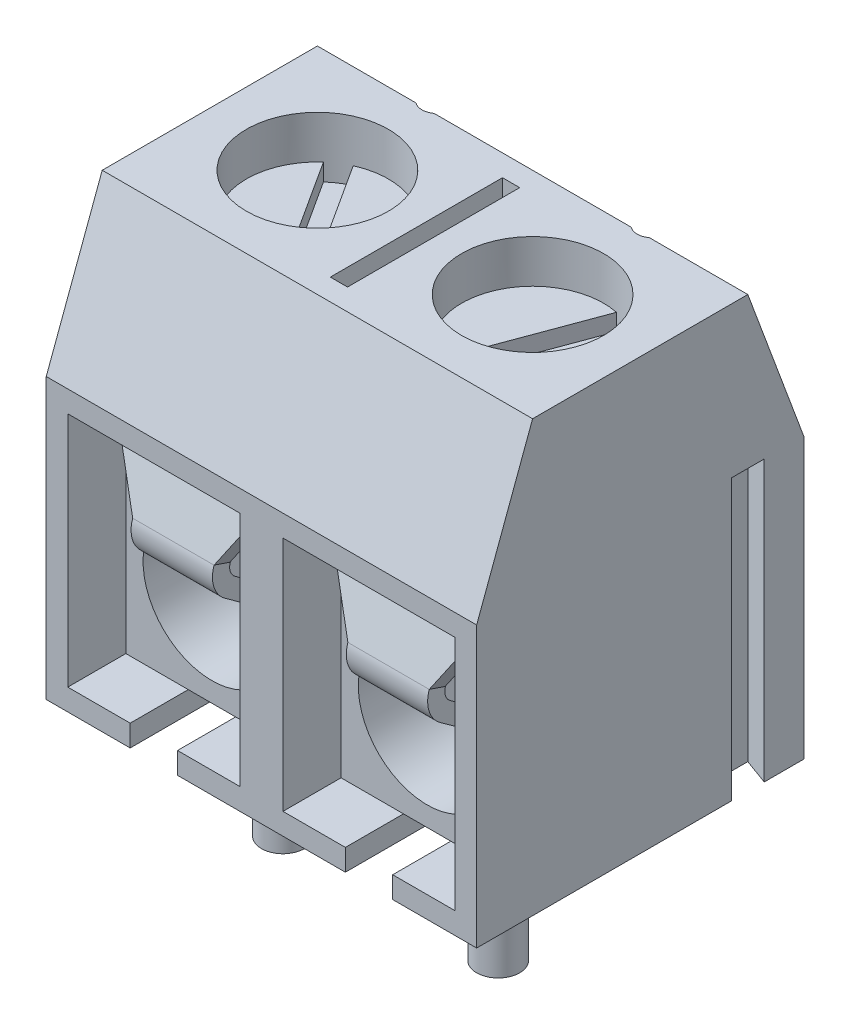
SolidWorks part; units mm, degrees
ref_plane "Front Plane" through (0, 0, 0) normal (0, 0, 1) x (1, 0, 0)
ref_plane "Top Plane" through (0, 0, 0) normal (0, 1, 0) x (1, 0, 0)
ref_plane "Right Plane" through (0, 0, 0) normal (1, 0, 0) x (0, 0, -1)
sketch "Sketch1" plane through (0, 0, 0) normal (0, 1, 0) x (1, 0, 0)
  line L1 (-5, 3.8) -> (5, 3.8)
  line L2 (-5, 3.8) -> (-5, -3.8)
  line L3 (-5, -3.8) -> (5, -3.8)
  line L4 (5, 3.8) -> (5, -3.8)
  dimension "D1" = 10
  dimension "D2" = 5
  dimension "D3" = 7.6
  dimension "D4" = 3.8
extrude "Extrude1" add sketch "Sketch1" along normal blind 10
sketch "Sketch2" plane through (0, 0, 0) normal (1, 0, 0) x (0, 0, -1)
  line L0 (2.5, 10) -> (3.8, 6.5)
  line L1 (3.8, 10) -> (-3.8, 10) construction
  line L2 (3.8, 10) -> (3.8, 0) construction
  line L3 (3.8, 6.5) -> (-3.8, 6.5) construction
  line L4 (-3.8, 10) -> (-3.8, 0) construction
  line L5 (-3.8, 6.5) -> (-2.5, 10)
  line L6 (-2.5, 10) -> (2.5, 10)
  line L7 (3.8, 6.5) -> (3.8, 0)
  line L8 (3.8, 0) -> (-3.8, 0)
  line L9 (-3.8, 0) -> (-3.8, 6.5)
  dimension "D1" = 5
  dimension "D2" = 2.5
  dimension "D3" = 3.5
extrude "Cut-Extrude1" cut sketch "Sketch2" against normal through all and the other way through all flip side to cut
sketch "Sketch3" plane through (0, 10, 0) normal (0, 1, 0) x (-1, 0, 0)
  line L0 (5, -2.5) -> (-5, -2.5) construction
  line L1 (0.2, -2) -> (-0.2, -2)
  line L2 (0.2, -2) -> (0.2, 2)
  line L3 (0.2, 2) -> (-0.2, 2)
  line L4 (-0.2, -2) -> (-0.2, 2)
  circle A0 centre (2.5, 0) radius 1.65
  circle A1 centre (-2.5, 0) radius 1.65
  circle A2 centre (2.5, -2.78) radius 0.35
  circle A3 centre (-2.5, -2.78) radius 0.35
  dimension "D7" = 3.3
  dimension "D8" = 0.7
  dimension "D1" = 0.4
  dimension "D2" = 0.2
  dimension "D3" = 4
  dimension "D4" = 2
  dimension "D5" = 2.5
  dimension "D6" = 2.5
  dimension "D9" = 0.28
extrude "Cut-Extrude2" cut sketch "Sketch3" against normal blind 4
sketch "Sketch4" plane through (0, 0, 3.8) normal (0, 0, 1) x (1, 0, 0)
  line L0 (-5, 6.5) -> (-5, 0) construction
  line L1 (-4.5, 6) -> (-0.5, 6)
  line L2 (-4.5, 6) -> (-4.5, 0.5)
  line L3 (-4.5, 0.5) -> (-0.5, 0.5)
  line L4 (-0.5, 6) -> (-0.5, 0.5)
  line L5 (0.5, 6) -> (4.5, 6)
  line L6 (0.5, 6) -> (0.5, 0.5)
  line L7 (0.5, 0.5) -> (4.5, 0.5)
  line L8 (4.5, 6) -> (4.5, 0.5)
  line L9 (-5, 6.5) -> (5, 6.5) construction
  line L10 (-5, 0) -> (5, 0) construction
  line L11 (5, 6.5) -> (5, 0) construction
  dimension "D1" = 0.5
  dimension "D2" = 0.5
  dimension "D3" = 0.5
  dimension "D4" = 1
  dimension "D5" = 0.5
extrude "Cut-Extrude3" cut sketch "Sketch4" against normal offset from surface (5.6 mm away) 2 up to face at (0, 3.25, -3.8)
sketch "Sketch5" plane through (0, 0, -1.8) normal (0, 0, 1) x (1, 0, 0)
  line L0 (-4.5, 5.6) -> (-0.5, 5.6)
  line L1 (0.5, 5.6) -> (4.5, 5.6)
  line L2 (-4.5, 5.6) -> (-4.5, 0.5)
  line L3 (-0.5, 5.6) -> (-0.5, 6) construction
  line L4 (-4.5, 6) -> (-4.5, 0.5)
  line L5 (-4.5, 0.5) -> (-0.5, 0.5)
  line L6 (-0.5, 0.5) -> (-0.5, 6)
  line L7 (-0.5, 6) -> (-4.5, 6)
  line L8 (-4.5, 6) -> (-4.5, 5.6) construction
  line L9 (-4.5, 0.5) -> (-0.5, 0.5)
  line L10 (-0.5, 0.5) -> (-0.5, 5.6)
  line L11 (-0.5, 6) -> (-4.5, 6) construction
  line L12 (0.5, 6) -> (0.5, 0.5)
  line L13 (0.5, 0.5) -> (4.5, 0.5)
  line L14 (4.5, 0.5) -> (4.5, 6)
  line L15 (4.5, 6) -> (0.5, 6)
  line L16 (0.5, 6) -> (0.5, 5.6) construction
  line L17 (0.5, 0.5) -> (4.5, 0.5)
  line L18 (4.5, 0.5) -> (4.5, 5.6)
  line L19 (4.5, 6) -> (0.5, 6) construction
  line L20 (0.5, 5.6) -> (0.5, 0.5)
  line L21 (4.5, 5.6) -> (4.5, 6) construction
  dimension "D3" = 0.4
  dimension "D1" = 0
  dimension "D2" = 0
extrude "Extrude2" add sketch "Sketch5" along normal offset from surface (4.25 mm away) 1.35 up to face at (2.5, 3.25, 3.8)
sketch "Sketch6" plane through (0, 0, 2.45) normal (0, 0, 1) x (1, 0, 0)
  circle A0 centre (-2.5, 2.5543) radius 1.6
  circle A1 centre (2.5, 2.5543) radius 1.6
  dimension "D1" = 3.2
extrude "Cut-Extrude4" cut sketch "Sketch6" against normal up to surface (4.25 mm away) up to face at (-2.5, 5.8, -1.8)
ref_plane "Plane1" through (-2.5, 0, 0) normal (1, 0, 0) x (0, 0, -1)
ref_plane "Plane2" through (2.5, 0, 0) normal (1, 0, 0) x (0, 0, -1)
sketch "Sketch7" plane through (0, 0, 0) normal (0, 1, 0) x (1, 0, 0)
  line L0 (-5, 2.5) -> (-5, -2.5) construction
  line L1 (-5.6, 3.1) -> (-5, 2.8816)
  line L2 (-5.6, 3.1) -> (-5.6, 1.9)
  line L3 (-5.6, 1.9) -> (-5, 2.1184)
  line L4 (-5, 2.8816) -> (-5, 2.1184)
  line L5 (5, 3.8) -> (-5, 3.8) construction
  dimension "D1" = 1.2
  dimension "D2" = 70
  dimension "D3" = 70
  dimension "D4" = 0.6
  dimension "D5" = 1.9
extrude "Extrude3" add sketch "Sketch7" along normal up to vertex (6.5 mm away) up to point (-5, 6.5, -3.8)
sketch "Sketch9" plane through (0, 0, 0) normal (0, 1, 0) x (1, 0, 0)
  line L0 (5, -3.8) -> (5, 3.8) construction
  line L8 (5, 2.8816) -> (4.4, 3.1)
  line L9 (5, 2.1184) -> (5, 2.8816)
  line L10 (4.4, 1.9) -> (5, 2.1184)
  line L11 (4.4, 3.1) -> (4.4, 1.9)
extrude "Cut-Extrude5" cut sketch "Sketch9" along normal up to vertex (6.5 mm away) up to point (5, 6.5, -3.8)
sketch "Sketch10" plane through (0, 0, 3.8) normal (0, 0, 1) x (1, 0, 0)
  line L0 (-4.5, 0.5) -> (-0.5, 0.5) construction
  line L1 (-3.05, 0.5) -> (-1.95, 0.5)
  line L2 (-3.05, 0.5) -> (-3.05, 0)
  line L3 (-3.05, 0) -> (-1.95, 0)
  line L4 (-1.95, 0.5) -> (-1.95, 0)
  line L5 (-5, 0) -> (5, 0) construction
  line L6 (0.5, 0.5) -> (4.5, 0.5) construction
  line L7 (1.95, 0.5) -> (3.05, 0.5)
  line L8 (1.95, 0.5) -> (1.95, 0)
  line L9 (1.95, 0) -> (3.05, 0)
  line L10 (3.05, 0.5) -> (3.05, 0)
  dimension "D1" = 1.1
  dimension "D2" = 0.55
  dimension "D3" = 0.55
extrude "Cut-Extrude6" cut sketch "Sketch10" against normal blind 3.6
sketch "Sketch11" plane through (0, 0.5, 0) normal (0, -1, 0) x (1, 0, 0)
  line L0 (-2.5, -1.8) -> (-2.5, 2.45) construction
  line L1 (2.5, -1.8) -> (2.5, 2.45) construction
  line L2 (-3.05, 0.2) -> (-1.95, 0.2) construction
  circle A0 centre (-2.5, 0.8) radius 0.5
  circle A1 centre (2.5, 0.8) radius 0.5
  dimension "D1" = 0.6
extrude "Extrude4" add sketch "Sketch11" along normal blind 3.5
sketch "Sketch12" plane through (0, 6, 0) normal (0, -1, 0) x (1, 0, 0)
  circle A0 centre (2.5, 0) radius 1.65 construction
  circle A1 centre (-2.5, 0) radius 1.65 construction
  circle A2 centre (2.5, 0) radius 1.65
  circle A3 centre (-2.5, 0) radius 1.65
extrude "Extrude5" add sketch "Sketch12" against normal offset from surface (3 mm away) 1 up to face at (0, 10, -1.2325)
sketch "Sketch13" plane through (0, 9, 0) normal (0, 1, 0) x (-1, 0, 0)
  line L1 (3.5943, -1.2349) -> (1.8258, 1.506)
  line L2 (3.1742, -1.506) -> (1.4057, 1.2349)
  line L5 (-2.8322, -1.6162) -> (-1.699, 1.4425)
  line L6 (-3.301, -1.4425) -> (-2.1678, 1.6162)
  circle A0 centre (-2.5, 0) radius 1.65 construction
  circle A1 centre (2.5, 0) radius 1.65 construction
  arc A2 (-1.699, 1.4425) -> (-2.1678, 1.6162) centre (-2.5, 0) ccw
  arc A3 (1.8258, 1.506) -> (1.4057, 1.2349) centre (2.5, 0) ccw
  arc A4 (-3.301, -1.4425) -> (-2.8322, -1.6162) centre (-2.5, 0) ccw
  arc A5 (3.1742, -1.506) -> (3.5943, -1.2349) centre (2.5, 0) ccw
  dimension "D1" = 0.5
  dimension "D2" = 0.5
extrude "Cut-Extrude7" cut sketch "Sketch13" against normal blind 0.4
sketch "Sketch14" plane through (-2.5, 0, 0) normal (-1, 0, 0) x (0, 0, 1)
  line L0 (2.45, 5.6) -> (3.0389, 3.8617)
  line L1 (3.0389, 3.8617) -> (0.1672, 1.7876)
  line L2 (0.1672, 1.7876) -> (-0.5464, 2.0974)
  line L3 (-0.5464, 2.0974) -> (-0.7057, 1.7305)
  line L4 (-0.7057, 1.7305) -> (0.2168, 1.33)
  line L5 (0.2168, 1.33) -> (3.5125, 3.7103)
  line L6 (-1.8, 5.6) -> (2.45, 5.6)
  line L7 (2.45, 5.6) -> (2.45, 0.5)
  line L8 (2.45, 0.5) -> (3.8, 0.5)
  line L9 (3.8, 0.5) -> (3.8, 6)
  line L10 (3.8, 6) -> (-1.8, 6)
  line L11 (-1.8, 6) -> (-1.8, 5.6)
  line L12 (-1.8, 5.6) -> (2.45, 5.6)
  line L13 (3.5125, 3.7103) -> (2.7368, 6)
  line L14 (2.7368, 6) -> (-1.8, 6)
  line L17 (-1.8, 6) -> (-1.8, 5.6)
  dimension "D2" = 0.4
  dimension "D3" = 0.4
  dimension "D4" = 0.4
  dimension "D1" = 0
extrude "Extrude6" add sketch "Sketch14" along normal blind 0.945 and the other way blind 0.945
sketch "Sketch15" plane through (0, 1.4494, 4.2784) normal (0, 0.3209, 0.9471) x (1, 0, 0)
  line L2 (-1.555, 4.8) -> (-1.555, 2.904)
  line L3 (-3.445, 4.8) -> (-3.445, 2.904)
  line L4 (-1.555, 2.904) -> (-0.51, 4.8)
  line L5 (-0.51, 4.8) -> (-1.555, 4.8)
  line L6 (-3.445, 2.904) -> (-4.49, 4.8)
  line L8 (-4.49, 4.8) -> (-3.445, 4.8)
extrude "Extrude9" add sketch "Sketch15" against normal blind 0.39
pattern_linear "LPattern1" count 2 spacing 5 along (1, 0, 0) of "Extrude6", "Extrude9"
fillet "Fillet1" radius 0.3 4 edges at (-2.5, 3.8617, 3.0389) (-2.5, 1.7876, 0.1672) (2.5, 1.7876, 0.1672) (2.5, 3.8617, 3.0389)
fillet "Fillet2" radius 0.7 4 edges at (-2.5, 3.7103, 3.5125) (-2.5, 1.33, 0.2168) (2.5, 1.33, 0.2168) (2.5, 3.7103, 3.5125)
sketch "Component_Outline" plane through (0, 0, 0) normal (0, 1, 0) x (1, 0, 0)
  line L0 (5, -3.8) -> (5, 3.8)
  line L1 (5, 3.8) -> (-5, 3.8)
  line L2 (-5, 3.8) -> (-5, 2.8816)
  line L3 (-5, 2.8816) -> (-5.6, 3.1)
  line L4 (-5.6, 3.1) -> (-5.6, 1.9)
  line L5 (-5.6, 1.9) -> (-5, 2.1184)
  line L6 (-5, 2.1184) -> (-5, -3.8)
  line L7 (-5, -3.8) -> (5, -3.8)
scale "Scale1" scale about origin uniform scaling yes scale factor 0.7
